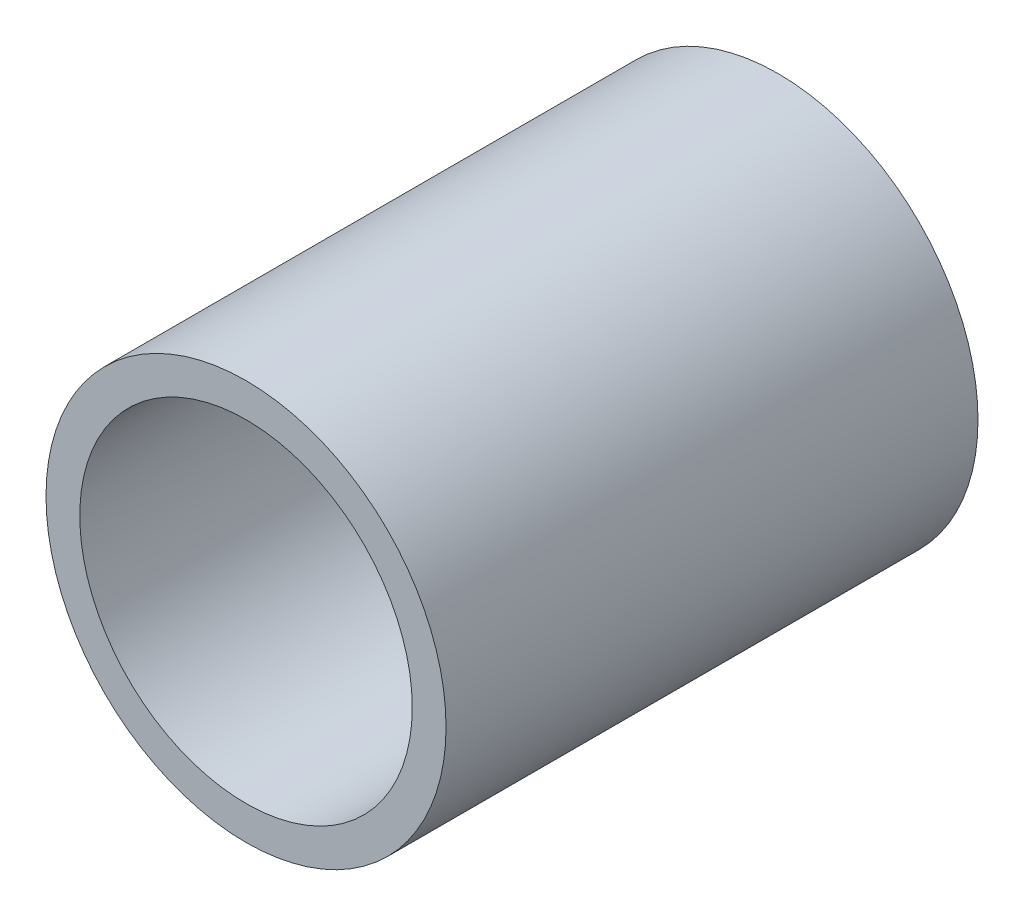
SolidWorks part; units mm, degrees
ref_plane "Front Plane" through (0, 0, 0) normal (0, 0, 1) x (1, 0, 0)
ref_plane "Top Plane" through (0, 0, 0) normal (0, 1, 0) x (1, 0, 0)
ref_plane "Right Plane" through (0, 0, 0) normal (1, 0, 0) x (0, 0, -1)
sketch "Sketch1" plane through (0, 0, 0) normal (0, 0, 1) x (1, 0, 0)
  circle A0 centre (0, 0) radius 4.7752
  circle A1 centre (0, 0) radius 3.9688
  dimension "D1" = 9.5504
  dimension "ID" = 7.9375
extrude "Extrude1" add sketch "Sketch1" along normal mid plane 12.7
sketch "Sketch2" plane through (0, 0, 0) normal (1, 0, 0) x (0, 0, -1)
  line L0 (-6.35, -3.9688) -> (6.35, -3.9688) construction
  line L3 (6.35, 3.9688) -> (-6.35, 3.9688) construction
  line L5 (-6.35, -3.9688) -> (6.35, -3.9688)
  line L6 (6.35, 3.9688) -> (-6.35, 3.9688)
sketch "Sketch4" plane through (0, 0, 6.35) normal (0, 0, 1) x (1, 0, 0)
  line L0 (0, 0) -> (-2.8063, 2.8063)
  line L1 (0, -6.1258) -> (0, 6.1258) construction
  circle A0 centre (0, 0) radius 3.9688 construction
  dimension "D1" = 45
